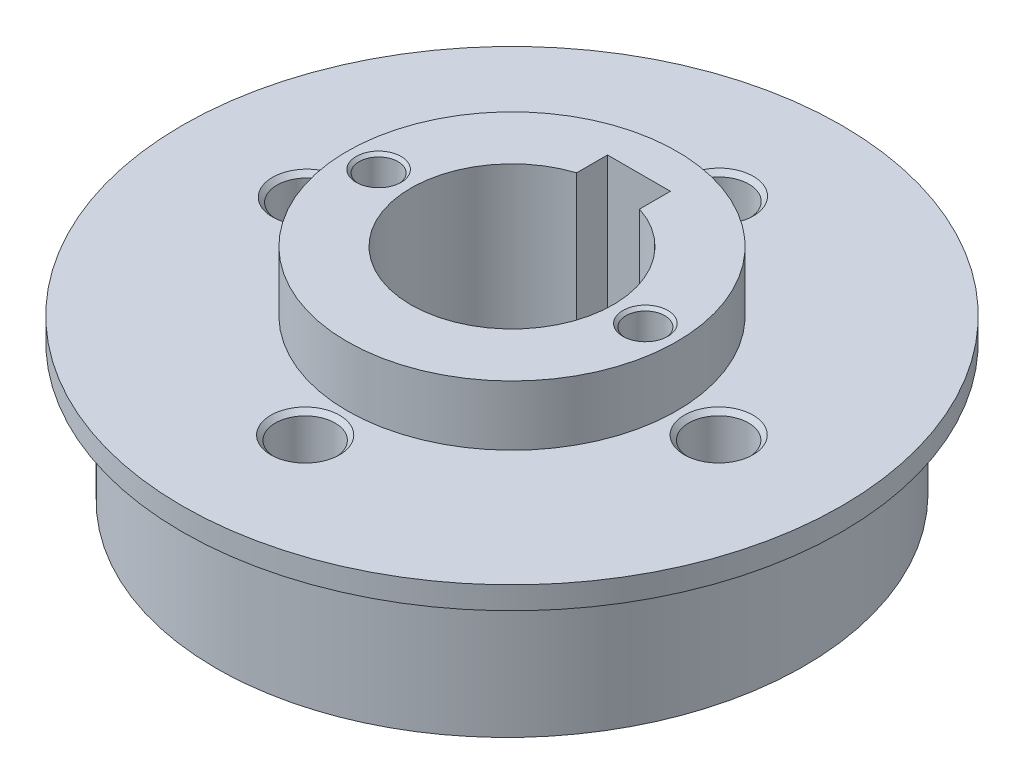
SolidWorks part; units mm, degrees
ref_plane "前视基准面" through (0, 0, 0) normal (0, 0, 1) x (1, 0, 0)
ref_plane "上视基准面" through (0, 0, 0) normal (0, 1, 0) x (1, 0, 0)
ref_plane "右视基准面" through (0, 0, 0) normal (1, 0, 0) x (0, 0, -1)
sketch "草图1" plane through (0, 0, 0) normal (0, 1, 0) x (1, 0, 0)
  circle A0 centre (0, 0) radius 22
extrude "凸台-拉伸1" add sketch "草图1" along normal blind 18.5
sketch "草图2" plane through (0, 18.5, 0) normal (0, 1, 0) x (1, 0, 0)
  circle A0 centre (0, 0) radius 11
  circle A1 centre (0, 0) radius 22
extrude "切除-拉伸1" cut sketch "草图2" against normal blind 4
sketch "草图4" plane through (0, 0, 0) normal (0, -1, 0) x (1, 0, 0)
  circle A0 centre (0, 0) radius 22
  ellipse E0 centre (0, 0) end of major axis (0, 19.75) minor radius 19.5
extrude "切除-拉伸2" cut sketch "草图4" against normal blind 13
sketch "草图5" plane through (0, 0, 0) normal (0, -1, 0) x (1, 0, 0)
  circle A0 centre (0, 0) radius 11
  circle A1 centre (0, 0) radius 21.652
extrude "切除-拉伸3" cut sketch "草图5" against normal blind 4
sketch "草图6" plane through (0, 18.5, 0) normal (0, 1, 0) x (1, 0, 0)
  line L1 (-2.0976, 8.4712) -> (2.0976, 8.4712)
  line L2 (-2.0976, 8.4712) -> (-2.0976, 6.4158)
  line L4 (2.0976, 8.4712) -> (2.0976, 6.4158)
  arc A0 (-2.0976, 6.4158) -> (2.0976, 6.4158) centre (0, 0) ccw
  point P2 (0, 6.75)
extrude "切除-拉伸4" cut sketch "草图6" against normal through all
hole_wizard "#1 螺旋的螺纹孔钻头1" positions "草图31" profile "草图32" hole size "#1-64" standard "ANSI Inch" end condition through all
sketch "草图31" plane through (0, 14.5, 0) normal (0, 1, 0) x (1, 0, 0)
  point P0 (0, 13.8103)
  point P2 (-85.4847, -69.8818)
  point P4 (13.7899, 0)
  point P6 (0, -13.801)
  point P8 (-13.6908, 0)
sketch "草图32" plane through (0, 14.5, -13.8103) normal (1, 0, 0) x (0, 0, 1)
  line L0 (0, 0) -> (0, 14.5)
  line L1 (0, 14.5) -> (1.9939, 14.5)
  line L2 (1.9939, 14.5) -> (1.9939, 0)
  line L5 (1.9939, 0) -> (0, 0)
  line L11 (0, -6.35) -> (0, 107.95) construction
  dimension "通孔孔直径" = 3.9878
  dimension "通孔孔深度" = 14.5
cosmetic thread "装饰螺纹线1" parameters "D2"=4.1
cosmetic thread "装饰螺纹线2" parameters "D2"=4.1
cosmetic thread "装饰螺纹线3" parameters "D2"=4.1
cosmetic thread "装饰螺纹线4" parameters "D2"=4.1
sketch "草图33" plane through (0, 18.5, 0) normal (0, 1, 0) x (1, 0, 0)
  circle A0 centre (0, 0) radius 8.9 construction
  circle A1 centre (8.9, 0) radius 1.3
  circle A2 centre (-8.9, 0) radius 1.3
extrude "切除-拉伸5" cut sketch "草图33" against normal blind 2.5
cosmetic thread "装饰螺纹线5" parameters "D2"=7.8
cosmetic thread "装饰螺纹线6" parameters "D2"=7.8
chamfer "倒角1" distance 0.3 angle 45 8 edges at (0, 4, -15.8042) (-13.6908, 4, -1.9939) (0, 4, 11.8071) (13.7899, 4, -1.9939) (-13.6908, 14.5, 1.9939) (0, 14.5, 15.7949) (13.7899, 14.5, 1.9939) (0, 14.5, -11.8164)
chamfer "倒角2" distance 0.2 angle 45 2 edges at (-8.9, 18.5, 1.3) (8.9, 18.5, 1.3)
